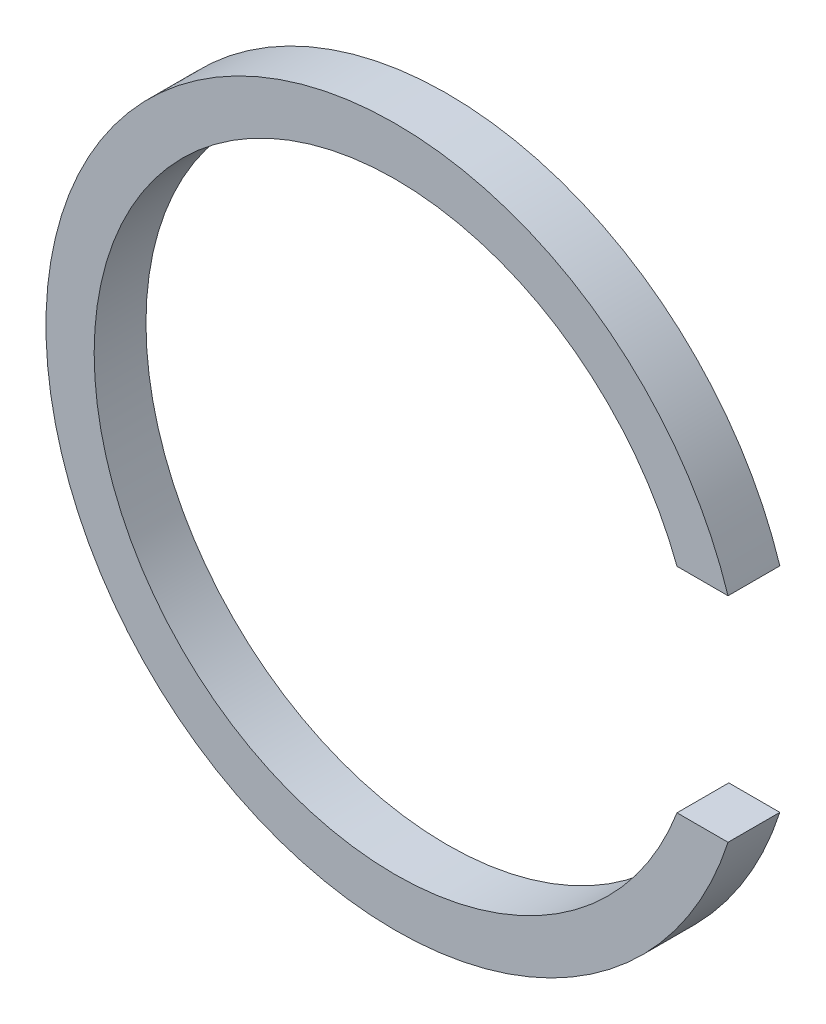
SolidWorks part; units mm, degrees
material "Silicon"
ref_plane "Front" through (0, 0, 0) normal (0, 0, 1) x (1, 0, 0)
ref_plane "Top" through (0, 0, 0) normal (0, 1, 0) x (1, 0, 0)
ref_plane "Right" through (0, 0, 0) normal (1, 0, 0) x (0, 0, -1)
sketch "Sketch1" plane through (0, 0, 0) normal (0, 0, 1) x (1, 0, 0)
  line L0 (70.1339, 26.575) -> (82.8418, 26.575)
  line L1 (70.1339, -26.575) -> (82.8418, -26.575)
  arc A0 (70.1339, 26.575) -> (70.1339, -26.575) centre (0, 0) ccw
  arc A2 (82.8418, 26.575) -> (82.8418, -26.575) centre (0, 0) ccw
extrude "Boss-Extrude1" add sketch "Sketch1" along normal blind 12.9 contours A0 L1 A2 L0
